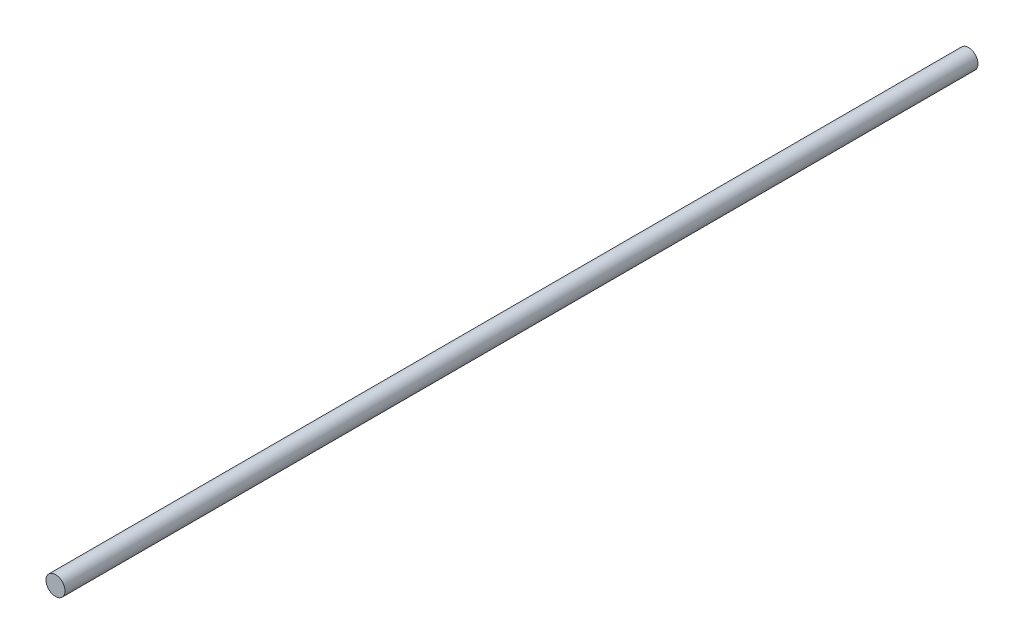
SolidWorks part; units mm, degrees
ref_plane "Front Plane" through (0, 0, 0) normal (0, 0, 1) x (1, 0, 0)
ref_plane "Top Plane" through (0, 0, 0) normal (0, 1, 0) x (1, 0, 0)
ref_plane "Right Plane" through (0, 0, 0) normal (1, 0, 0) x (0, 0, -1)
sketch "Sketch1" plane through (0, 0, 0) normal (0, 0, 1) x (1, 0, 0)
  circle A0 centre (0, 0) radius 3.175
  dimension "D1" = 6.35
extrude "Boss-Extrude1" add sketch "Sketch1" along normal blind 304.8
